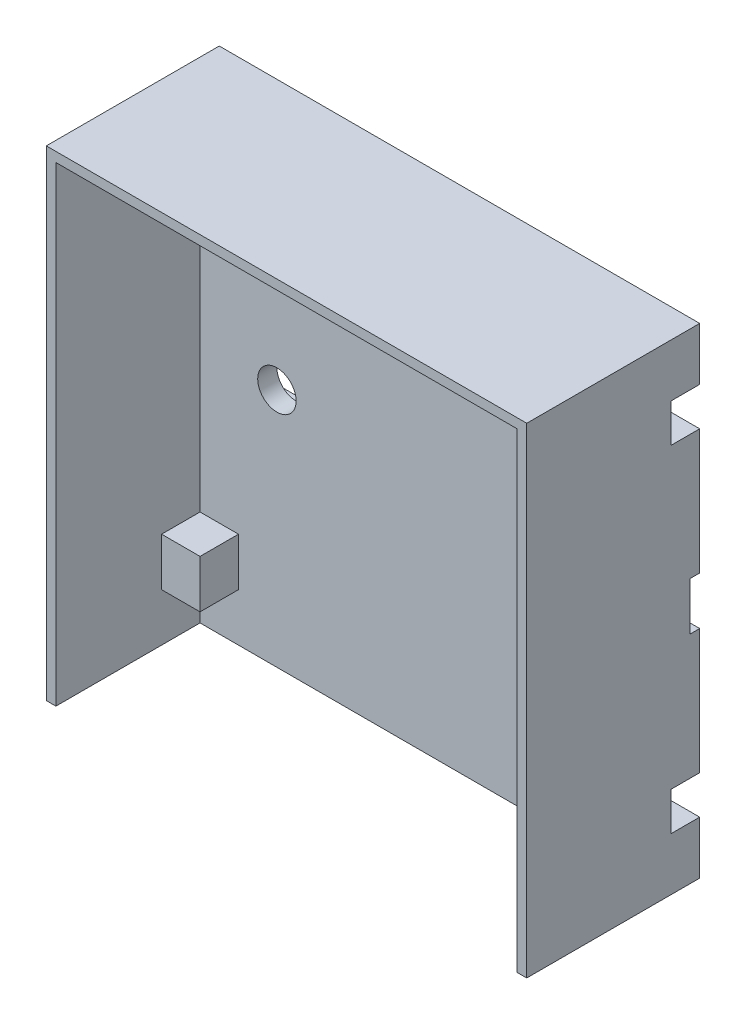
SolidWorks part; units mm, degrees
ref_plane "Přední rovina" through (0, 0, 0) normal (0, 0, 1) x (1, 0, 0)
ref_plane "Horní rovina" through (0, 0, 0) normal (0, 1, 0) x (1, 0, 0)
ref_plane "Pravá rovina" through (0, 0, 0) normal (1, 0, 0) x (0, 0, -1)
sketch "Skica1" plane through (0, 0, 0) normal (0, 0, 1) x (1, 0, 0)
  line L1 (25, 25) -> (-25, 25)
  line L2 (25, 25) -> (25, -25)
  line L3 (25, -25) -> (-25, -25)
  line L4 (-25, 25) -> (-25, -25)
  line L5 (25, 25) -> (-25, -25) construction
  line L6 (25, -25) -> (-25, 25) construction
  point P0 (0, 0)
  point P5 (-27.5, 0)
  point P11 (4.5, 0)
  dimension "D1" = 50
  dimension "D2" = 50
extrude "Přidat vysunutím2" add sketch "Skica1" along normal blind 3 contours L2 L1 L4 L3
sketch "Skica5" plane through (0, 0, 0) normal (0, 0, -1) x (-1, 0, 0)
  line L10 (25, 25) -> (25, -25) construction
  line L11 (-25, 2.5) -> (25, 2.5)
  line L12 (-25, 2.5) -> (-25, -2.5)
  line L13 (-25, -2.5) -> (25, -2.5)
  line L14 (25, 2.5) -> (25, -2.5)
  line L15 (-25, 2.5) -> (25, -2.5) construction
  line L16 (-25, -2.5) -> (25, 2.5) construction
  point P0 (0, 0)
  dimension "D1" = 5
extrude "Odebrat vysunutím3" cut sketch "Skica5" against normal blind 1 contours L11 L14 L13 L12
sketch "Skica14" plane through (0, 0, 3) normal (0, 0, 1) x (1, 0, 0)
  line L1 (-25, 25) -> (25, 25)
  line L2 (-25, 25) -> (-25, -25)
  line L3 (-25, -25) -> (25, -25)
  line L4 (25, 25) -> (25, -25)
  line L5 (-24, 24) -> (24, 24)
  line L6 (-24, 24) -> (-24, -25)
  line L7 (-24, -25) -> (24, -25)
  line L8 (24, 24) -> (24, -25)
  line M13 (-25, -25) -> (25, -25)
  line M14 (25, -25) -> (25, 25)
  line M15 (25, 25) -> (-25, 25)
  line M16 (-25, 25) -> (-25, -25)
  dimension "D1" = 1
  dimension "D2" = 1
  dimension "D3" = 1
  dimension "D4" = 0
extrude "Přidat vysunutím9" add sketch "Skica14" along normal blind 15 contours L5 L8 L6 M13 M14 M15 M16
sketch "Skica17" plane through (0, 0, 1) normal (0, 0, -1) x (-1, 0, 0)
  line L0 (-25, 2.5) -> (-25, -2.5) construction
  line L1 (-10, -2.5) -> (-10, 2.5) construction
  line L2 (25, 2.5) -> (25, -2.5) construction
  circle A0 centre (-16, 0) radius 2
  circle A1 centre (16, 0) radius 2
  dimension "D1" = 4
  dimension "D2" = 4
  dimension "D3" = 9
  dimension "D4" = 6
  dimension "D5" = 9
extrude "Odebrat vysunutím8" cut sketch "Skica17" against normal blind 4
sketch "Skica18" plane through (0, 0, 0) normal (0, 0, -1) x (-1, 0, 0)
  line L0 (-25, 25) -> (-25, 2.5) construction
  line L1 (0, -69.6084) -> (0, 55.4747) construction
  line L2 (46.798, 0) -> (-48.9089, 0) construction
  line L3 (-25, 20) -> (-20, 20)
  line L4 (-25, 20) -> (-25, 15)
  line L5 (-25, 15) -> (-20, 15)
  line L6 (-20, 20) -> (-20, 15)
  line L7 (-25, 25) -> (25, 25) construction
  line L8 (-25, -15) -> (-20, -15)
  line L9 (-20, -20) -> (-20, -15)
  line L10 (-25, -20) -> (-20, -20)
  line L11 (-25, -20) -> (-25, -15)
  line L12 (25, -20) -> (25, -15)
  line L13 (25, -20) -> (20, -20)
  line L14 (20, -20) -> (20, -15)
  line L15 (25, -15) -> (20, -15)
  line L16 (25, 15) -> (20, 15)
  line L17 (20, 20) -> (20, 15)
  line L18 (25, 20) -> (20, 20)
  line L19 (25, 20) -> (25, 15)
  dimension "D1" = 5
  dimension "D2" = 5
extrude "Přidat vysunutím10" add sketch "Skica18" against normal blind 7
sketch "Skica19" plane through (0, 0, 0) normal (0, 0, -1) x (-1, 0, 0)
  line L0 (0, 41.3732) -> (0, -50.234) construction
  line L1 (-48.8027, 0) -> (43.4862, 0) construction
  line L2 (-25, 25) -> (-25, 2.5) construction
  line L3 (-25, 19.5) -> (-21, 19.5)
  line L4 (-25, 19.5) -> (-25, 15.5)
  line L5 (-25, 15.5) -> (-21, 15.5)
  line L6 (-21, 19.5) -> (-21, 15.5)
  line L7 (-25, 25) -> (25, 25) construction
  line L8 (-25, -15.5) -> (-21, -15.5)
  line L9 (-21, -19.5) -> (-21, -15.5)
  line L10 (-25, -19.5) -> (-21, -19.5)
  line L11 (-25, -19.5) -> (-25, -15.5)
  line L12 (25, -19.5) -> (25, -15.5)
  line L13 (25, -19.5) -> (21, -19.5)
  line L14 (21, -19.5) -> (21, -15.5)
  line L15 (25, -15.5) -> (21, -15.5)
  line L16 (25, 15.5) -> (21, 15.5)
  line L17 (21, 19.5) -> (21, 15.5)
  line L18 (25, 19.5) -> (21, 19.5)
  line L19 (25, 19.5) -> (25, 15.5)
  dimension "D1" = 4
  dimension "D2" = 5.5
extrude "Odebrat vysunutím9" cut sketch "Skica19" against normal blind 3
sketch "Skica20" plane through (0, 0, 3) normal (0, 0, -1) x (-1, 0, 0)
  line L0 (-21, 15.5) -> (-21, 19.5) construction
  line L1 (-21, 19.5) -> (-25, 19.5) construction
  line L2 (0, 36.4573) -> (0, -43.1233) construction
  line L3 (38.443, 0) -> (-42.4315, 0) construction
  circle A0 centre (-22.75, 17.5) radius 1.25
  circle A1 centre (22.75, 17.5) radius 1.25
  circle A2 centre (22.75, -17.5) radius 1.25
  circle A3 centre (-22.75, -17.5) radius 1.25
  dimension "D1" = 2.5
  dimension "D2" = 1.75
  dimension "D3" = 2
extrude "Odebrat vysunutím10" cut sketch "Skica20" against normal blind 3
